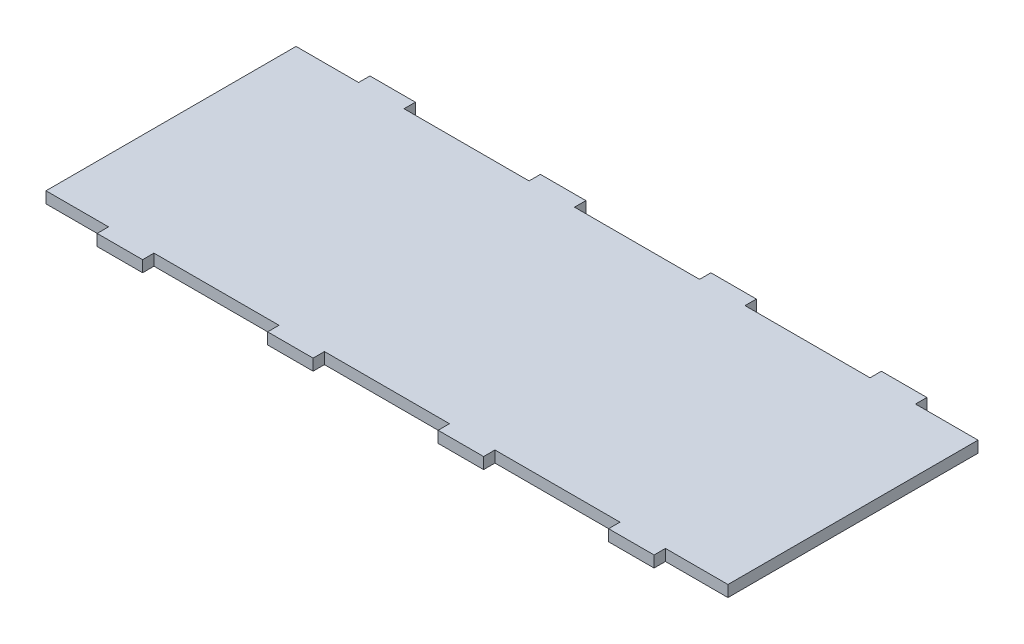
SolidWorks part; units mm, degrees
material "Cedar"
ref_plane "Front Plane" through (0, 0, 0) normal (0, 0, 1) x (1, 0, 0)
ref_plane "Top Plane" through (0, 0, 0) normal (0, 1, 0) x (1, 0, 0)
ref_plane "Right Plane" through (0, 0, 0) normal (1, 0, 0) x (0, 0, -1)
sketch "Sketch1" plane through (0, 0, 0) normal (0, 1, 0) x (1, 0, 0)
  line L1 (-190.5, 76.2) -> (190.5, 76.2)
  line L2 (-190.5, 76.2) -> (-190.5, -76.2)
  line L3 (-190.5, -76.2) -> (190.5, -76.2)
  line L4 (190.5, 76.2) -> (190.5, -76.2)
  line L5 (-190.5, 76.2) -> (190.5, -76.2) construction
  line L6 (-190.5, -76.2) -> (190.5, 76.2) construction
  point P0 (0, 0)
  dimension "D1" = 152.4
  dimension "D2" = 381
extrude "Boss-Extrude1" add sketch "Sketch1" along normal blind 6.35
sketch "Sketch2" plane through (0, 6.35, 0) normal (0, 1, 0) x (1, 0, 0)
  line L0 (-190.5, -69.85) -> (190.5, -69.85) construction
  line L1 (-190.5, 76.2) -> (-190.5, -76.2) construction
  line L2 (190.5, -76.2) -> (190.5, 76.2) construction
  line L3 (-190.5, -76.2) -> (190.5, -76.2) construction
  line L5 (-34.925, -69.85) -> (34.925, -69.85)
  line L6 (-34.925, -69.85) -> (-34.925, -76.2)
  line L7 (-34.925, -76.2) -> (34.925, -76.2)
  line L8 (34.925, -69.85) -> (34.925, -76.2)
  line L9 (-34.925, -69.85) -> (34.925, -76.2) construction
  line L10 (-34.925, -76.2) -> (34.925, -69.85) construction
  point P8 (0, -73.025)
  point P14 (0, -69.85)
  point P18 (0, -69.85)
  dimension "D1" = 6.35
  dimension "D2" = 69.85
extrude "Cut-Extrude2" cut sketch "Sketch2" against normal through all
pattern_linear "LPattern1" count 3 spacing 95.25 along (-1, 0, 0) count 3 spacing 95.25 along (1, 0, 0) of "Cut-Extrude2"
mirror "Mirror2" about plane through (0, 0, 0) normal (0, 0, 1) of "LPattern1", "Cut-Extrude2"
